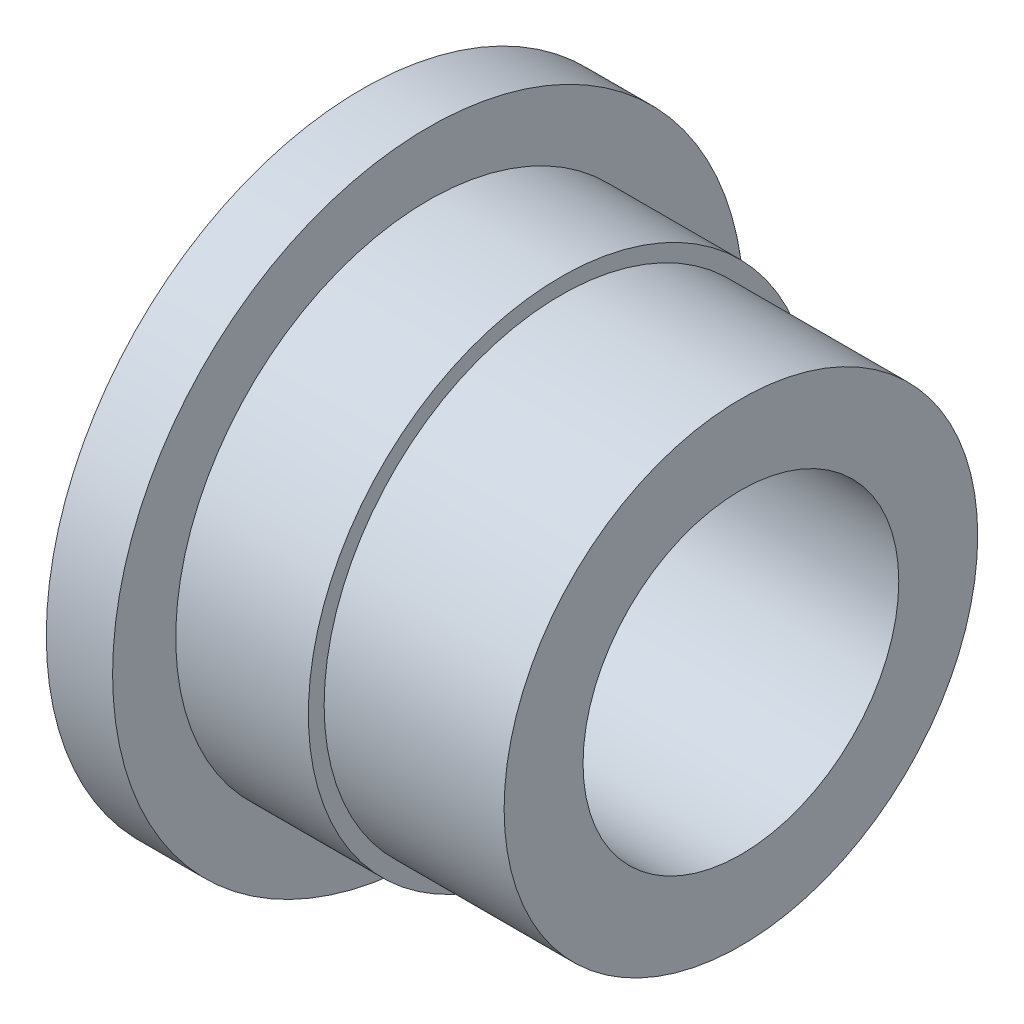
SolidWorks part; units mm, degrees
ref_plane "Front" through (0, 0, 0) normal (0, 0, 1) x (1, 0, 0)
ref_plane "Top" through (0, 0, 0) normal (0, 1, 0) x (1, 0, 0)
ref_plane "Right" through (0, 0, 0) normal (1, 0, 0) x (0, 0, -1)
sketch "Sketch1" plane through (0, 0, 0) normal (0, 0, 1) x (1, 0, 0)
  line L0 (0, 5) -> (0, 7.5)
  line L1 (0, 7.5) -> (-5.7, 7.5)
  line L2 (-5.7, 7.5) -> (-5.7, 8)
  line L3 (-5.7, 8) -> (-9.9, 8)
  line L4 (-9.9, 8) -> (-9.9, 10)
  line L5 (-9.9, 10) -> (-12, 10)
  line L6 (-12, 10) -> (-12, 5)
  line L7 (-12, 5) -> (0, 5)
  line L8 (0, 0) -> (-15.6846, 0) construction
  dimension "D1" = 2.5
  dimension "D2" = 0.5
  dimension "D3" = 2
  dimension "D4" = 12
  dimension "D5" = 2.1
  dimension "D6" = 4.2
  dimension "D7" = 5
revolve "Base-Revolve" add sketch "Sketch1" angle 360 about L8
